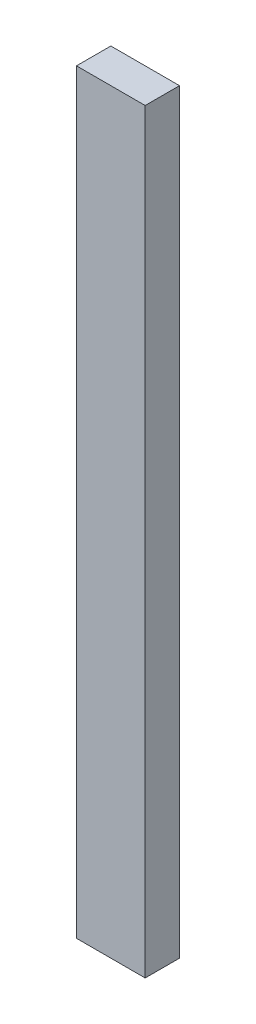
SolidWorks part; units mm, degrees
ref_plane "Plane1" through (0, 0, 0) normal (0, 0, 1) x (1, 0, 0)
ref_plane "Plane2" through (0, 0, 0) normal (0, 1, 0) x (1, 0, 0)
ref_plane "Plane3" through (0, 0, 0) normal (1, 0, 0) x (0, 0, -1)
sketch "Sketch1" plane through (0, 0, 0) normal (0, 0, 1) x (1, 0, 0)
  line L1 (0, 0) -> (20, 0)
  line L2 (0, 0) -> (0, 220)
  line L3 (0, 220) -> (20, 220)
  line L4 (20, 0) -> (20, 220)
  dimension "D1" = 220
  dimension "D2" = 20
extrude "Boss-Extrude1" add sketch "Sketch1" along normal blind 10
